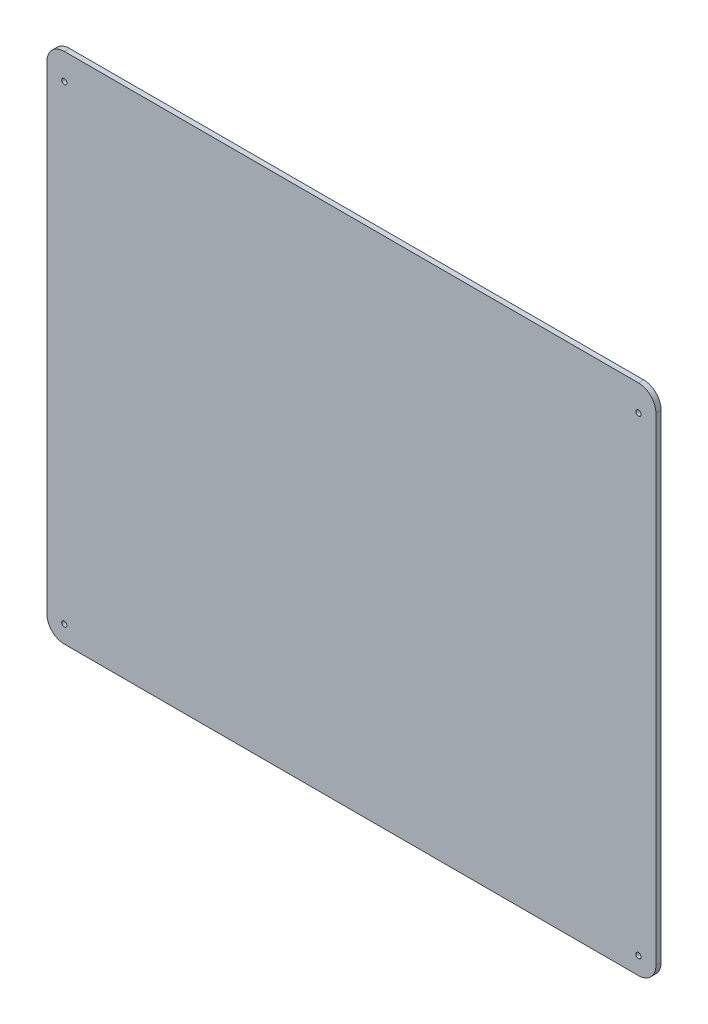
SolidWorks part; units mm, degrees
ref_plane "Plan de face" through (0, 0, 0) normal (0, 0, 1) x (1, 0, 0)
ref_plane "Plan de dessus" through (0, 0, 0) normal (0, 1, 0) x (1, 0, 0)
ref_plane "Plan de droite" through (0, 0, 0) normal (1, 0, 0) x (0, 0, -1)
sketch "Esquisse1" plane through (0, 0, 0) normal (0, 0, 1) x (1, 0, 0)
  line L1 (10, 0) -> (340, 0)
  line L2 (0, 10) -> (0, 285)
  line L3 (10, 295) -> (340, 295)
  line L4 (350, 10) -> (350, 285)
  arc A0 (10, 0) -> (0, 10) centre (10, 10) cw
  arc A1 (340, 0) -> (350, 10) centre (340, 10) ccw
  arc A2 (340, 295) -> (350, 285) centre (340, 285) cw
  arc A3 (0, 285) -> (10, 295) centre (10, 285) cw
  circle A4 centre (340, 280) radius 1.5
  circle A5 centre (10, 280) radius 1.5
  circle A6 centre (10, 10) radius 1.5
  circle A7 centre (340, 10) radius 1.5
  point P7 (0, 0)
  point P10 (350, 0)
  point P15 (0, 295)
  dimension "D3" = 10
  dimension "D4" = 3
  dimension "D7" = 3
  dimension "D10" = 3
  dimension "D13" = 3
  dimension "D1" = 295
  dimension "D2" = 350
  dimension "D5" = 15
  dimension "D6" = 10
  dimension "D8" = 15
  dimension "D9" = 10
  dimension "D11" = 10
  dimension "D12" = 10
  dimension "D14" = 10
  dimension "D15" = 10
  dimension "D16" = 270
  dimension "D17" = 270
  dimension "D25" = 330
extrude "Boss.-Extru.1" add sketch "Esquisse1" along normal blind 3
